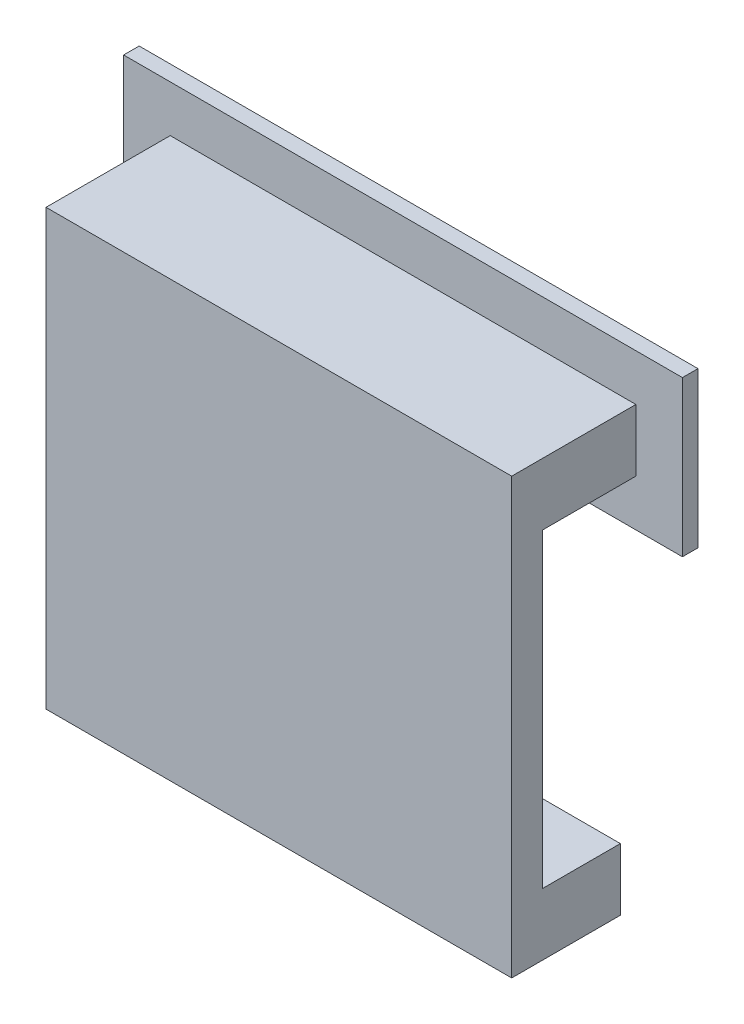
SolidWorks part; units mm, degrees
ref_plane "Front Plane" through (0, 0, 0) normal (0, 0, 1) x (1, 0, 0)
ref_plane "Top Plane" through (0, 0, 0) normal (0, 1, 0) x (1, 0, 0)
ref_plane "Right Plane" through (0, 0, 0) normal (1, 0, 0) x (0, 0, -1)
sketch "Sketch1" plane through (0, 0, 0) normal (0, 0, 1) x (1, 0, 0)
  line L1 (-19.05, 2.54) -> (19.05, 2.54)
  line L2 (-19.05, 2.54) -> (-19.05, -2.54)
  line L3 (-19.05, -2.54) -> (19.05, -2.54)
  line L4 (19.05, 2.54) -> (19.05, -2.54)
  line L5 (-19.05, 2.54) -> (19.05, -2.54) construction
  line L6 (-19.05, -2.54) -> (19.05, 2.54) construction
  point P0 (0, 0)
  dimension "D1" = 38.1
  dimension "D2" = 5.08
extrude "Boss-Extrude1" add sketch "Sketch1" along normal blind 2.54
sketch "Sketch2" plane through (0, 2.54, 0) normal (0, 1, 0) x (1, 0, 0)
  line L1 (-19.05, 0) -> (19.05, 0)
  line L2 (-19.05, 0) -> (-19.05, -2.54)
  line L3 (-19.05, -2.54) -> (19.05, -2.54)
  line L4 (19.05, 0) -> (19.05, -2.54)
  line L5 (-19.05, 0) -> (19.05, -2.54) construction
  line L6 (-19.05, -2.54) -> (19.05, 0) construction
  point P0 (0, -1.27)
  dimension "D1" = 2.54
  dimension "D2" = 38.1
extrude "Boss-Extrude2" add sketch "Sketch2" along normal blind 30.48
sketch "Sketch3" plane through (0, 0, 0) normal (0, 0, -1) x (-1, 0, 0)
  line L1 (-19.05, 27.94) -> (19.05, 27.94)
  line L2 (-19.05, 27.94) -> (-19.05, 33.02)
  line L3 (-19.05, 33.02) -> (19.05, 33.02)
  line L4 (19.05, 27.94) -> (19.05, 33.02)
  line L5 (-19.05, 27.94) -> (19.05, 33.02) construction
  line L6 (-19.05, 33.02) -> (19.05, 27.94) construction
  point P0 (0, 30.48)
  dimension "D1" = 5.08
  dimension "D2" = 38.1
extrude "Boss-Extrude3" add sketch "Sketch3" along normal blind 7.62
sketch "Sketch4" plane through (0, 0, 0) normal (0, 0, -1) x (-1, 0, 0)
  line L1 (-19.05, 2.54) -> (19.05, 2.54)
  line L2 (-19.05, 2.54) -> (-19.05, -2.54)
  line L3 (-19.05, -2.54) -> (19.05, -2.54)
  line L4 (19.05, 2.54) -> (19.05, -2.54)
  line L5 (-19.05, 2.54) -> (19.05, -2.54) construction
  line L6 (-19.05, -2.54) -> (19.05, 2.54) construction
  point P0 (0, 0)
extrude "Boss-Extrude4" add sketch "Sketch4" along normal blind 6.35
sketch "Sketch5" plane through (0, 0, -7.62) normal (0, 0, -1) x (-1, 0, 0)
  line L0 (-19.05, 33.02) -> (-19.05, 27.94) construction
  line L1 (-22.86, 36.83) -> (22.86, 36.83)
  line L2 (-22.86, 36.83) -> (-22.86, 24.13)
  line L3 (-22.86, 24.13) -> (22.86, 24.13)
  line L4 (22.86, 36.83) -> (22.86, 24.13)
  line L5 (-22.86, 36.83) -> (22.86, 24.13) construction
  line L6 (-22.86, 24.13) -> (22.86, 36.83) construction
  point P0 (0, 30.48)
  point P9 (-19.05, 30.48)
  dimension "D1" = 12.7
  dimension "D2" = 45.72
extrude "Boss-Extrude5" add sketch "Sketch5" along normal blind 1.27
